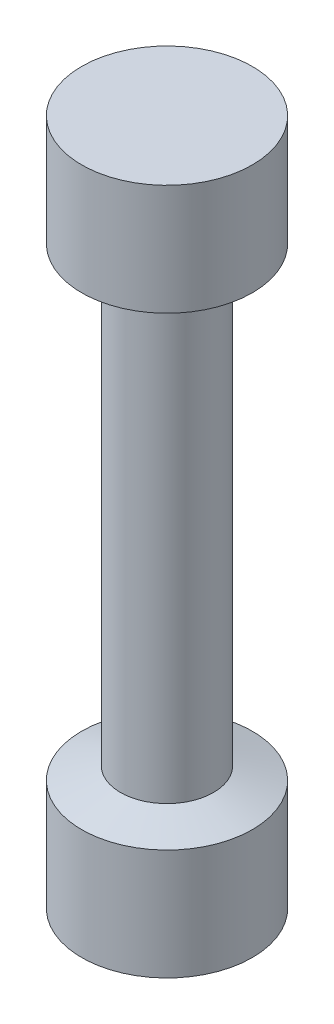
SolidWorks part; units mm, degrees
ref_plane "Plano frontal" through (0, 0, 0) normal (0, 0, 1) x (1, 0, 0)
ref_plane "Plano superior" through (0, 0, 0) normal (0, 1, 0) x (1, 0, 0)
ref_plane "Plano direito" through (0, 0, 0) normal (1, 0, 0) x (0, 0, -1)
sketch "Esboço2" plane through (0, 0, 0) normal (0, 0, 1) x (1, 0, 0)
  line L0 (0, -28.7093) -> (0, 1406.7566) construction
  line L1 (-6.7, 8.7) -> (-3.65, 9.7)
  line L2 (0, 0) -> (-6.7, 0)
  line L3 (0, 0) -> (0, 8.7)
  line L4 (0, 8.7) -> (-6.7, 8.7)
  line L5 (-6.7, 0) -> (-6.7, 8.7)
  line L6 (0, 8.7) -> (-3.65, 8.7)
  line L7 (0, 8.7) -> (0, 45.2)
  line L8 (0, 26.95) -> (-3.65, 26.95)
  line L9 (-3.65, 8.7) -> (-3.65, 45.2)
  line L10 (-1000, 26.95) -> (49000, 26.95) construction
  line L11 (-6.7, 45.2) -> (-3.65, 44.2)
  line L12 (0, 45.2) -> (-6.7, 45.2)
  line L13 (-6.7, 53.9) -> (-6.7, 45.2)
  line L14 (0, 53.9) -> (-6.7, 53.9)
  line L15 (0, 53.9) -> (0, 45.2)
  line L16 (0, 45.2) -> (-3.65, 45.2)
  dimension "D1" = 6.7
  dimension "D2" = 8.7
  dimension "D3" = 1
  dimension "D5" = 18.25
  dimension "D6" = 3.65
revolve "Revolução1" add sketch "Esboço2" angle 360 about L0
sketch "Esboço3" plane through (0, 0, 0) normal (0, 0, 1) x (1, 0, 0)
  line L0 (0, -1000) -> (0, 49000) construction
